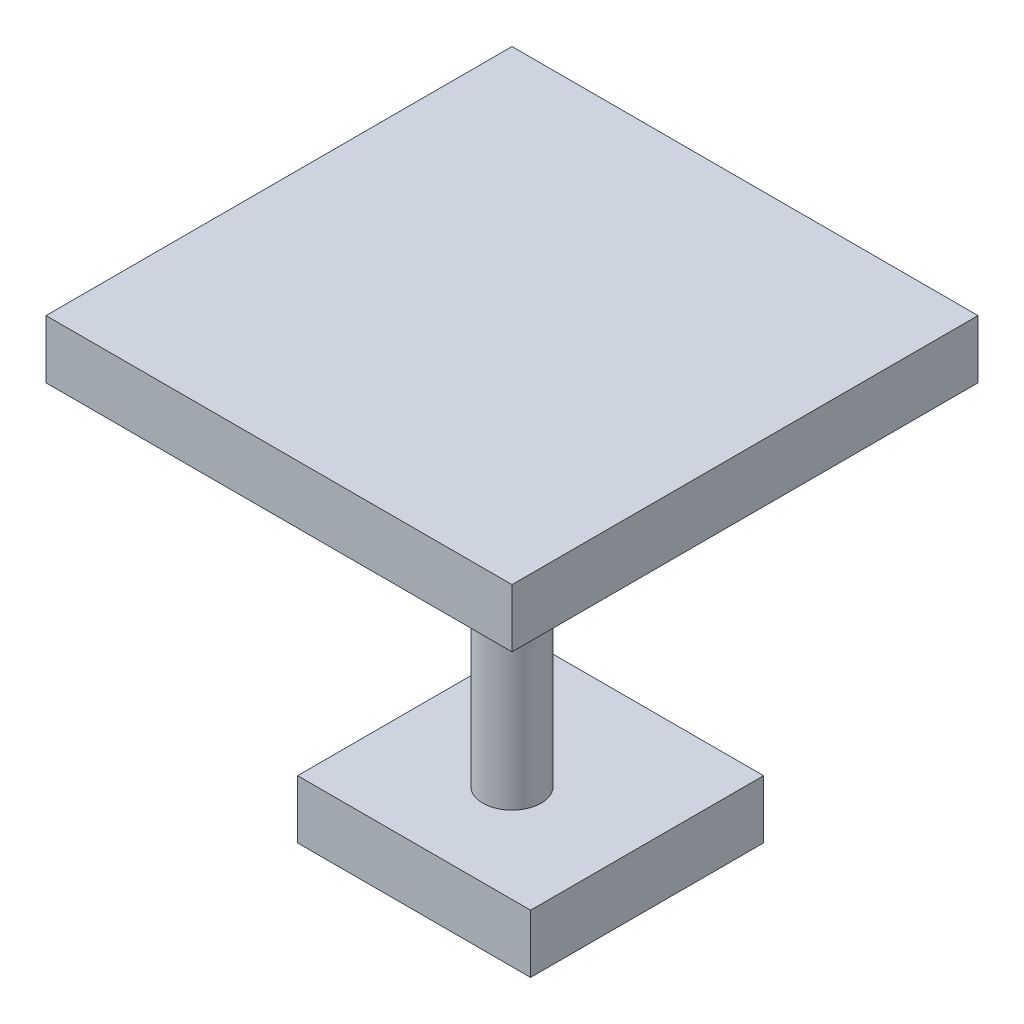
SolidWorks part; units mm, degrees
ref_plane "Front Plane" through (0, 0, 0) normal (0, 0, 1) x (1, 0, 0)
ref_plane "Top Plane" through (0, 0, 0) normal (0, 1, 0) x (1, 0, 0)
ref_plane "Right Plane" through (0, 0, 0) normal (1, 0, 0) x (0, 0, -1)
sketch "Sketch1" plane through (0, 0, 0) normal (0, 1, 0) x (1, 0, 0)
  line L1 (0, 0) -> (20, 0)
  line L2 (0, 0) -> (0, -20)
  line L3 (0, -20) -> (20, -20)
  line L4 (20, 0) -> (20, -20)
  circle A1 centre (10, -10) radius 2.5
  dimension "D1" = 20
  dimension "D2" = 20
extrude "Boss-Extrude3" add sketch "Sketch1" along normal blind 30 contours A1
sketch "Sketch4" plane through (0, 30, 0) normal (0, 1, 0) x (1, 0, 0)
  line L3 (-10, 10) -> (30, 10)
  line L4 (-10, 10) -> (-10, -30)
  line L5 (-10, -30) -> (30, -30)
  line L6 (30, 10) -> (30, -30)
  dimension "D1" = 40
  dimension "D2" = 40
extrude "Boss-Extrude5" add sketch "Sketch4" along normal blind 5
sketch "Sketch5" plane through (0, 0, 0) normal (0, -1, 0) x (1, 0, 0)
  line L3 (20, 18.4051) -> (0, 18.4051)
  line L4 (20, 18.4051) -> (20, -1.5949)
  line L5 (20, -1.5949) -> (0, -1.5949)
  line L6 (0, 18.4051) -> (0, -1.5949)
  dimension "D1" = 20
  dimension "D2" = 20
extrude "Boss-Extrude6" add sketch "Sketch5" along normal blind 5
